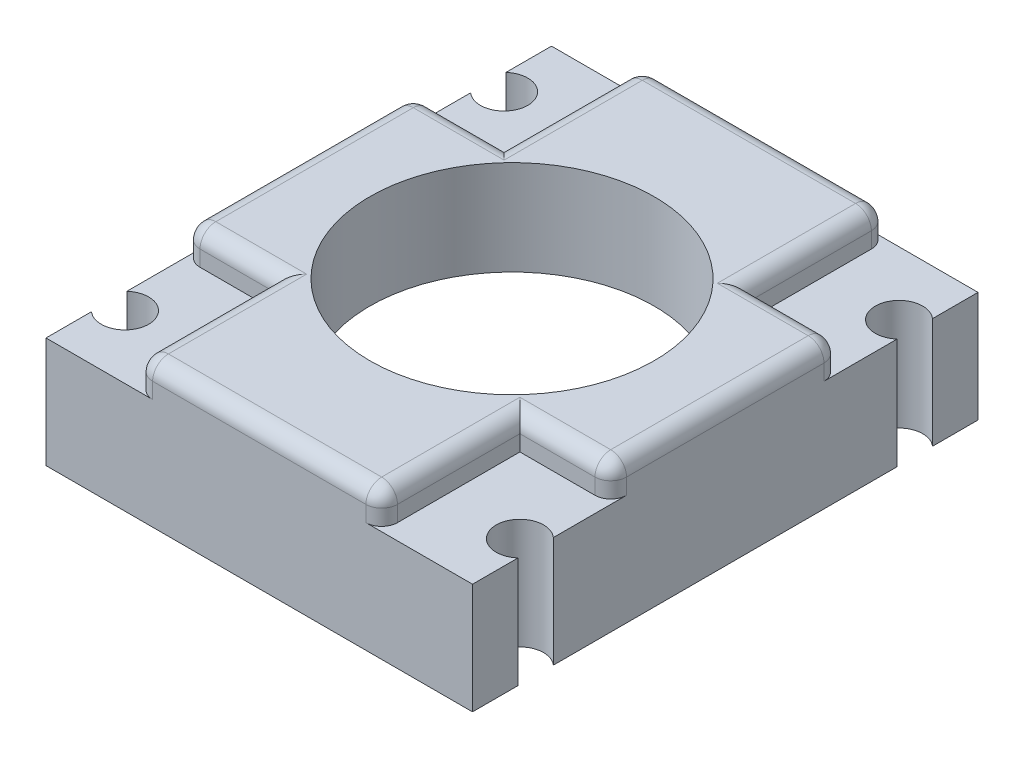
SolidWorks part; units mm, degrees
ref_plane "Front Plane" through (0, 0, 0) normal (0, 0, 1) x (1, 0, 0)
ref_plane "Top Plane" through (0, 0, 0) normal (0, 1, 0) x (1, 0, 0)
ref_plane "Right Plane" through (0, 0, 0) normal (1, 0, 0) x (0, 0, -1)
sketch "Sketch1" plane through (0, 0, 0) normal (0, 1, 0) x (1, 0, 0)
  line L0 (0, 0) -> (0, 15) construction
  line L1 (0, 15) -> (-12.5, 15) construction
  line L2 (-12.5, 15) -> (-12.5, -15) construction
  line L3 (-12.5, -15) -> (12.5, -15) construction
  line L4 (12.5, -15) -> (12.5, 15) construction
  line L5 (12.5, 15) -> (0, 15) construction
  line L6 (-12.5, 15) -> (-12.5, 12) construction
  line L7 (-12.5, -15) -> (-12.5, -12) construction
  line L8 (12.5, -15) -> (12.5, -12) construction
  line L9 (12.5, 15) -> (12.5, 12) construction
  circle A0 centre (-12.5, 12) radius 1.5
  circle A1 centre (12.5, 12) radius 1.5
  circle A2 centre (-12.5, -12) radius 1.5
  circle A3 centre (12.5, -12) radius 1.5
  dimension "D9" = 3
  dimension "D10" = 3
  dimension "D11" = 3
  dimension "D12" = 3
  dimension "D1" = 15
  dimension "D2" = 12.5
  dimension "D3" = 30
  dimension "D4" = 25
  dimension "D5" = 3
  dimension "D6" = 3
  dimension "D7" = 3
  dimension "D8" = 3
sketch "Sketch2" plane through (0, 0, 0) normal (0, 1, 0) x (1, 0, 0)
  line L1 (-13.5, -16) -> (13.5, -16)
  line L2 (-13.5, -16) -> (-13.5, 16)
  line L3 (-13.5, 16) -> (13.5, 16)
  line L4 (13.5, -16) -> (13.5, 16)
  line L5 (-13.5, -16) -> (13.5, 16) construction
  line L6 (-13.5, 16) -> (13.5, -16) construction
  circle A0 centre (0, 0) radius 9
  dimension "D1" = 18
  dimension "D2" = 27
  dimension "D3" = 32
extrude "Boss-Extrude1" add sketch "Sketch2" along normal blind 6
sketch "Sketch3" plane through (0, 0, 0) normal (0, -1, 0) x (1, 0, 0)
  line L1 (-13.5, -16) -> (13.5, -16)
  line L2 (-13.5, -16) -> (-13.5, 16)
  line L3 (-13.5, 16) -> (13.5, 16)
  line L4 (13.5, -16) -> (13.5, 16)
  line L5 (-13.5, -16) -> (13.5, 16) construction
  line L6 (-13.5, 16) -> (13.5, -16) construction
  line L7 (-12.5, -15) -> (12.5, -15)
  line L8 (-12.5, -15) -> (-12.5, 15)
  line L9 (-12.5, 15) -> (12.5, 15)
  line L10 (12.5, -15) -> (12.5, 15)
  line L11 (-12.5, -15) -> (12.5, 15) construction
  line L12 (-12.5, 15) -> (12.5, -15) construction
  point P0 (0, 0)
  point P7 (0, 0)
extrude "Boss-Extrude2" add sketch "Sketch3" along normal blind 3
extrude "Cut-Extrude1" cut sketch "Sketch1" against normal through all both and the other way through all
sketch "Sketch5" plane through (0, -3, 0) normal (0, -1, 0) x (1, 0, 0)
  line L0 (13.5, -10.882) -> (13.5, -9.7087)
  line L1 (13.5, -10.882) -> (13.5, 10.882) construction
  line L2 (13.5, -13.118) -> (13.5, -14.2913)
  line L3 (13.5, -16) -> (13.5, -13.118) construction
  arc A2 (13.5, -10.882) -> (13.5, -13.118) centre (12.5, -12) ccw
  arc A3 (13.5, -9.7087) -> (13.5, -14.2913) centre (12.5, -12) ccw
  dimension "D1" = 5
extrude "Boss-Extrude4" add sketch "Sketch5" against normal up to next (9 mm away)
mirror "Mirror1" about plane through (0, 0, 0) normal (1, 0, 0) of "Boss-Extrude4"
mirror "Mirror2" about plane through (0, 0, 0) normal (0, 0, 1) of "Mirror1", "Boss-Extrude4"
sketch "Sketch6" plane through (0, 6, 0) normal (0, 1, 0) x (1, 0, 0)
  circle A0 centre (12.5, 12) radius 2.8
  dimension "D1" = 5.6
extrude "Cut-Extrude2" cut sketch "Sketch6" against normal blind 2
mirror "Mirror3" about plane through (0, 0, 0) normal (1, 0, 0) of "Cut-Extrude2"
mirror "Mirror4" about plane through (0, 0, 0) normal (0, 0, 1) of "Mirror3", "Cut-Extrude2"
fillet "Fillet1" radius 1 6 edges at (13.5, 6, -15.3077) (13.5, 6, 15.3077) (-13.5, 6, 15.3077) (-13.5, 6, -15.3077) (0, 6, -16) (0, 6, 16)
sketch "Sketch11" plane through (0, 6, 0) normal (0, 1, 0) x (1, 0, 0)
  line L1 (-17.25, -16.75) -> (-7.75, -16.75)
  line L2 (-17.25, -16.75) -> (-17.25, -7.25)
  line L3 (-17.25, -7.25) -> (-7.75, -7.25)
  line L4 (-7.75, -16.75) -> (-7.75, -7.25)
  line L5 (-17.25, -16.75) -> (-7.75, -7.25) construction
  line L6 (-17.25, -7.25) -> (-7.75, -16.75) construction
  point P0 (-12.5, -12)
  dimension "D1" = 9.5
  dimension "D2" = 9.5
extrude "Cut-Extrude3" cut sketch "Sketch11" against normal blind 2
mirror "Mirror5" about plane through (0, 0, 0) normal (1, 0, 0) of "Cut-Extrude3"
mirror "Mirror6" about plane through (0, 0, 0) normal (0, 0, 1) of "Mirror5", "Cut-Extrude3"
fillet "Fillet2" radius 1 24 edges at (-13.2071, 5.7071, 7.25) (-7.75, 5.7071, 15.7071) (-7.75, 4.5, 16) (-13.5, 4.5, 7.25) (-7.75, 6, 11.125) (-10.125, 6, 7.25) (13.2071, 5.7071, 7.25) (7.75, 5.7071, 15.7071) (7.75, 6, 11.125) (10.125, 6, 7.25) (7.75, 4.5, 16) (13.5, 4.5, 7.25) (7.75, 5.7071, -15.7071) (13.2071, 5.7071, -7.25) (13.5, 4.5, -7.25) (7.75, 4.5, -16) (7.75, 6, -11.125) (10.125, 6, -7.25) (-13.2071, 5.7071, -7.25) (-7.75, 5.7071, -15.7071) (-7.75, 6, -11.125) (-10.125, 6, -7.25) (-7.75, 4.5, -16) (-13.5, 4.5, -7.25)
